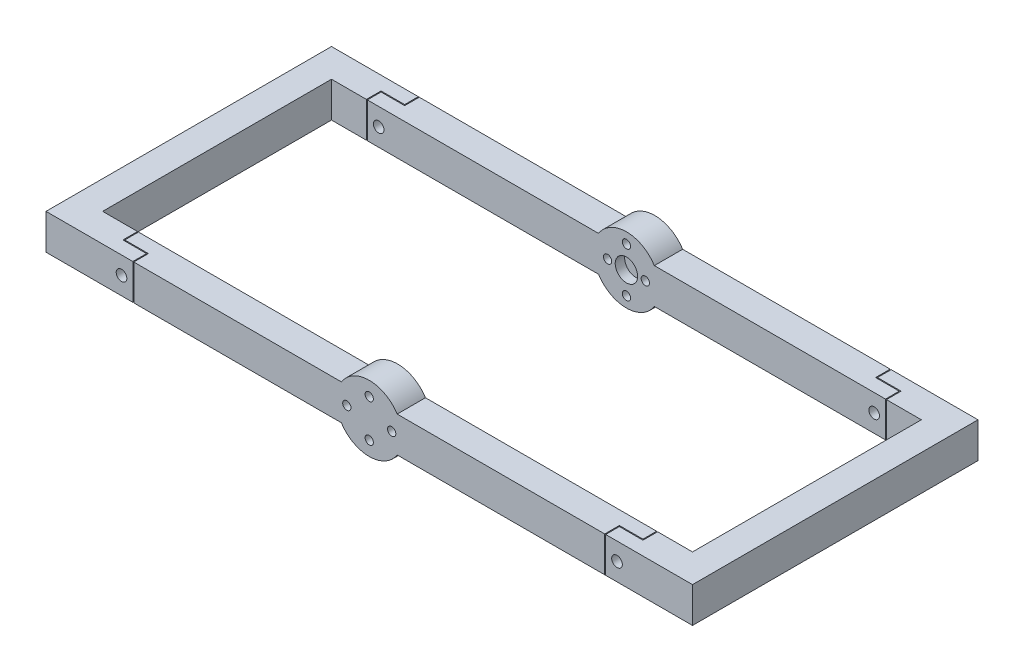
SolidWorks part; units mm, degrees
ref_plane "Front Plane" through (0, 0, 0) normal (0, 0, 1) x (1, 0, 0)
ref_plane "Top Plane" through (0, 0, 0) normal (0, 1, 0) x (1, 0, 0)
ref_plane "Right Plane" through (0, 0, 0) normal (1, 0, 0) x (0, 0, -1)
sketch "Sketch2" plane through (0, 0, 12) normal (0, 0, -1) x (-1, 0, 0)
  circle A0 centre (0, 0) radius 14
  dimension "D1" = 28
extrude "Boss-Extrude1" add sketch "Sketch2" along normal blind 12
sketch "Sketch10" plane through (0, 0, 0) normal (1, 0, 0) x (0, 0, -1)
  line L0 (-12, 14) -> (-12, -14) construction
  line L1 (-12, 7.5) -> (0, 7.5)
  line L2 (-12, 7.5) -> (-12, -7.5)
  line L3 (-12, -7.5) -> (0, -7.5)
  line L4 (0, 7.5) -> (0, -7.5)
  point P4 (0, 0)
  point P6 (-12, -5.6426)
  dimension "D1" = 15
extrude "Boss-Extrude5" add sketch "Sketch10" along normal blind 137
sketch "Sketch11" plane through (0, 0, 12) normal (0, 0, 1) x (1, 0, 0)
  line L0 (137, -7.5) -> (11.8216, -7.5) construction
  line L1 (137, 7.5) -> (125, 7.5)
  line L2 (137, 7.5) -> (137, -7.5)
  line L3 (137, -7.5) -> (125, -7.5)
  line L4 (125, 7.5) -> (125, -7.5)
  dimension "D1" = 12
extrude "Boss-Extrude6" add sketch "Sketch11" along normal up to surface (97 mm away)
sketch "Sketch12" plane through (137, 0, 0) normal (1, 0, 0) x (0, 0, -1)
  line L1 (-109, -7.5) -> (-121, -7.5)
  line L2 (-109, -7.5) -> (-109, 7.5)
  line L3 (-109, 7.5) -> (-121, 7.5)
  line L4 (-121, -7.5) -> (-121, 7.5)
  point P5 (-109, 7.5)
  dimension "D1" = 12
extrude "Boss-Extrude7" add sketch "Sketch12" against normal up to surface (137 mm away) up to plane "Right Plane"
sketch "Sketch13" plane through (0, 0, 109) normal (0, 0, 1) x (1, 0, 0)
  line L0 (0, 7.5) -> (0, -7.5) construction
  circle A0 centre (0, 0) radius 14
  dimension "D1" = 28
extrude "Boss-Extrude8" add sketch "Sketch13" along normal up to surface (12 mm away) up to face at (68.5, 0, 121)
mirror "Mirror6" about plane through (0, 0, 0) normal (1, 0, 0) of "Boss-Extrude7", "Boss-Extrude6", "Boss-Extrude5"
sketch "Sketch4" plane through (0, 0, 12) normal (0, 0, 1) x (1, 0, 0)
  circle A0 centre (0, 0) radius 4.75
  dimension "D1" = 9.5
extrude "Cut-Extrude2" cut sketch "Sketch4" against normal blind 4
sketch "Sketch3" plane through (0, 0, 12) normal (0, 0, 1) x (1, 0, 0)
  circle A0 centre (8, 0) radius 1.75
  circle A1 centre (0, -9.5) radius 1.75
  circle A2 centre (-8, 0) radius 1.75
  circle A3 centre (0, 9.5) radius 1.75
  dimension "D1" = 3.5
  dimension "D2" = 3.5
  dimension "D3" = 3.5
  dimension "D4" = 3.5
extrude "Cut-Extrude1" cut sketch "Sketch3" against normal through all
sketch "Sketch14" plane through (0, 0, 109) normal (0, 0, -1) x (-1, 0, 0)
  circle A0 centre (0, 0) radius 4.75
  dimension "D1" = 9.5
extrude "Cut-Extrude3" cut sketch "Sketch14" against normal blind 4
sketch "Sketch15" plane through (0, 0, 109) normal (0, 0, -1) x (-1, 0, 0)
  circle A0 centre (-9.5, 0) radius 1.75
  circle A1 centre (0, 8) radius 1.75
  circle A2 centre (9.5, 0) radius 1.75
  circle A3 centre (0, -8) radius 1.75
  dimension "D1" = 3.5
  dimension "D2" = 3.5
  dimension "D3" = 3.5
  dimension "D4" = 3.5
extrude "Cut-Extrude4" cut sketch "Sketch15" against normal through all
sketch "Sketch16" plane through (0, 7.5, 0) normal (0, 1, 0) x (1, 0, 0)
  line L0 (100, 0) -> (100, -6) construction
  line L1 (137, 0) -> (11.8216, 0) construction
  line L2 (100, -6) -> (110, -6) construction
  line L3 (110, -6) -> (110, -12) construction
  line L4 (125, -12) -> (11.8216, -12) construction
  line L5 (100, 0) -> (100, 10) construction
  line L6 (125, 0) -> (125, -12) construction
  line L7 (0, 0) -> (0, -121) construction
  line L8 (-11.8216, -121) -> (11.8216, -121) construction
  line L9 (0, -60.5) -> (137, -60.5) construction
  line L11 (137, 0) -> (137, -121) construction
  line L12 (99.8, 0) -> (99.8, -6.2)
  line L13 (99.8, -6.2) -> (109.8, -6.2)
  line L14 (109.8, -6.2) -> (109.8, -12)
  line L15 (100.2, 0) -> (100.2, -5.8)
  line L16 (100.2, -5.8) -> (110.2, -5.8)
  line L17 (110.2, -5.8) -> (110.2, -12)
  line L18 (99.8, 0) -> (100.2, 0)
  line L19 (109.8, -12) -> (110.2, -12)
  line L20 (109.8, -109) -> (110.2, -109)
  line L21 (110.2, -115.2) -> (110.2, -109)
  line L22 (109.8, -114.8) -> (109.8, -109)
  line L23 (99.8, -114.8) -> (109.8, -114.8)
  line L24 (100.2, -115.2) -> (110.2, -115.2)
  line L25 (100.2, -121) -> (100.2, -115.2)
  line L26 (99.8, -121) -> (99.8, -114.8)
  line L27 (99.8, -121) -> (100.2, -121)
  line L28 (-99.8, -121) -> (-100.2, -121)
  line L29 (-99.8, -121) -> (-99.8, -114.8)
  line L30 (-100.2, -121) -> (-100.2, -115.2)
  line L31 (-100.2, -115.2) -> (-110.2, -115.2)
  line L32 (-99.8, -114.8) -> (-109.8, -114.8)
  line L33 (-109.8, -114.8) -> (-109.8, -109)
  line L34 (-110.2, -115.2) -> (-110.2, -109)
  line L35 (-109.8, -109) -> (-110.2, -109)
  line L36 (-109.8, -12) -> (-110.2, -12)
  line L37 (-109.8, -6.2) -> (-109.8, -12)
  line L38 (-110.2, -5.8) -> (-110.2, -12)
  line L39 (-99.8, -6.2) -> (-109.8, -6.2)
  line L40 (-100.2, -5.8) -> (-110.2, -5.8)
  line L41 (-99.8, 0) -> (-99.8, -6.2)
  line L42 (-100.2, 0) -> (-100.2, -5.8)
  line L43 (-99.8, 0) -> (-100.2, 0)
  point P12 (125, -6)
  dimension "D1" = 10
  dimension "D2" = 0.2
  dimension "D3" = 0.2
extrude "Cut-Extrude5" cut sketch "Sketch16" against normal through all
sketch "Sketch17" plane through (0, 0, 0) normal (0, 0, -1) x (-1, 0, 0)
  line L0 (-99.8, -7.5) -> (-110.2, 7.5) construction
  line L1 (-137, 7.5) -> (-100.2, 7.5) construction
  circle A0 centre (-105, 0) radius 2.25
  point P8 (-102.5612, -3.5175)
  point P9 (0, 0)
  point P10 (-105, 0)
  dimension "D1" = 4.5
extrude "Cut-Extrude6" cut sketch "Sketch17" against normal through all
mirror "Mirror7" about plane through (0, 0, 0) normal (1, 0, 0) of "Cut-Extrude6"
